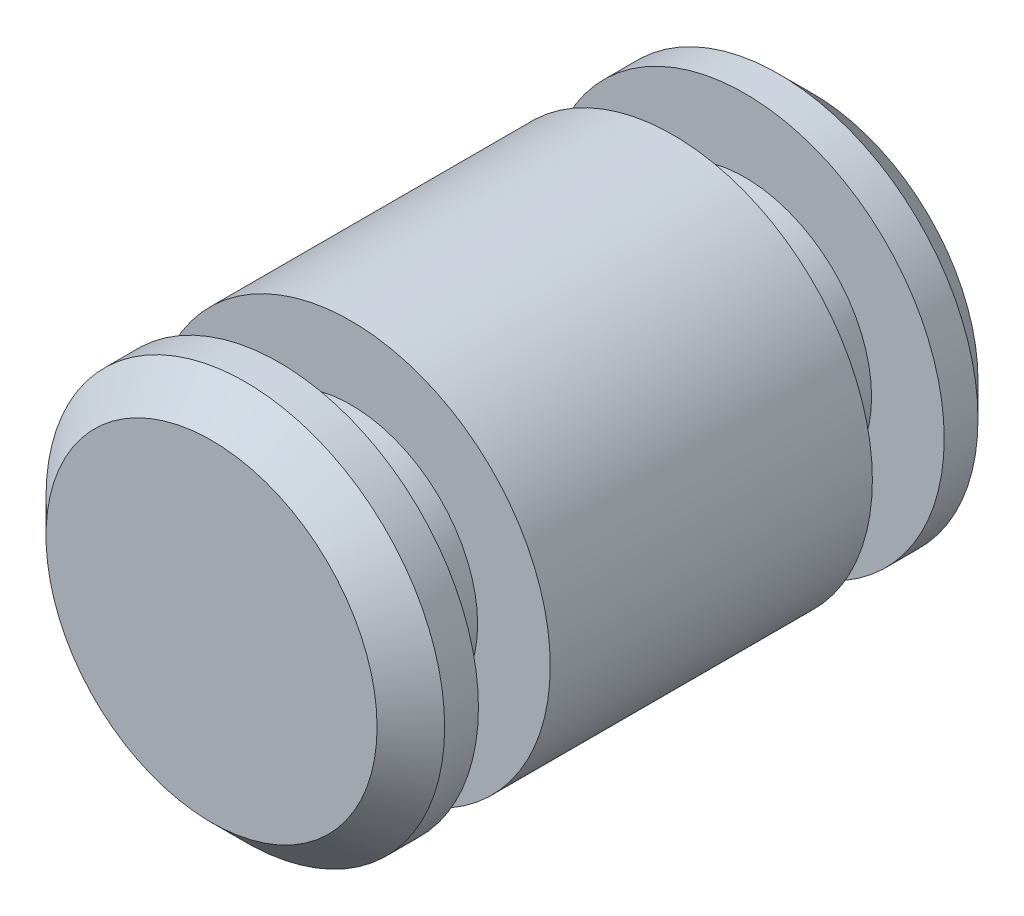
SolidWorks part; units mm, degrees
material "AISI Type A2 Tool Steel"
ref_plane "Front Plane" through (0, 0, 0) normal (0, 0, 1) x (1, 0, 0)
ref_plane "Top Plane" through (0, 0, 0) normal (0, 1, 0) x (1, 0, 0)
ref_plane "Right Plane" through (0, 0, 0) normal (1, 0, 0) x (0, 0, -1)
sketch "Sketch1" plane through (0, 0, 0) normal (0, 0, 1) x (1, 0, 0)
  circle A0 centre (0, 0) radius 1.4986
  dimension "D1" = 2.9972
extrude "Boss-Extrude1" add sketch "Sketch1" along normal mid plane 4.518
sketch "Sketch2" plane through (0, 0, 0) normal (1, 0, 0) x (0, 0, -1)
  line L0 (-2.259, -1.4986) -> (2.259, -1.4986) construction
  line L1 (-1.751, -1.4986) -> (-1.211, -1.4986)
  line L2 (-1.751, -1.4986) -> (-1.751, -0.9525)
  line L3 (-1.751, -0.9525) -> (-1.211, -0.9525)
  line L4 (-1.211, -1.4986) -> (-1.211, -0.9525)
  line L5 (-2.259, 1.4986) -> (-2.259, -1.4986) construction
  line L6 (-8.828, 0) -> (8.9454, 0) construction
  line L7 (1.6485, 0) -> (-1.6485, 0) construction
  line L8 (0, 2.428) -> (0, -3.7184) construction
  line L9 (1.211, -1.4986) -> (1.211, -0.9525)
  line L10 (1.751, -0.9525) -> (1.211, -0.9525)
  line L11 (1.751, -1.4986) -> (1.751, -0.9525)
  line L12 (1.751, -1.4986) -> (1.211, -1.4986)
  dimension "D1" = 0.508
  dimension "D2" = 0.54
  dimension "D3" = 1.905
revolve "Cut-Revolve1" cut sketch "Sketch2" angle 360 about L6
chamfer "Chamfer1" distance 0.254 angle 45
